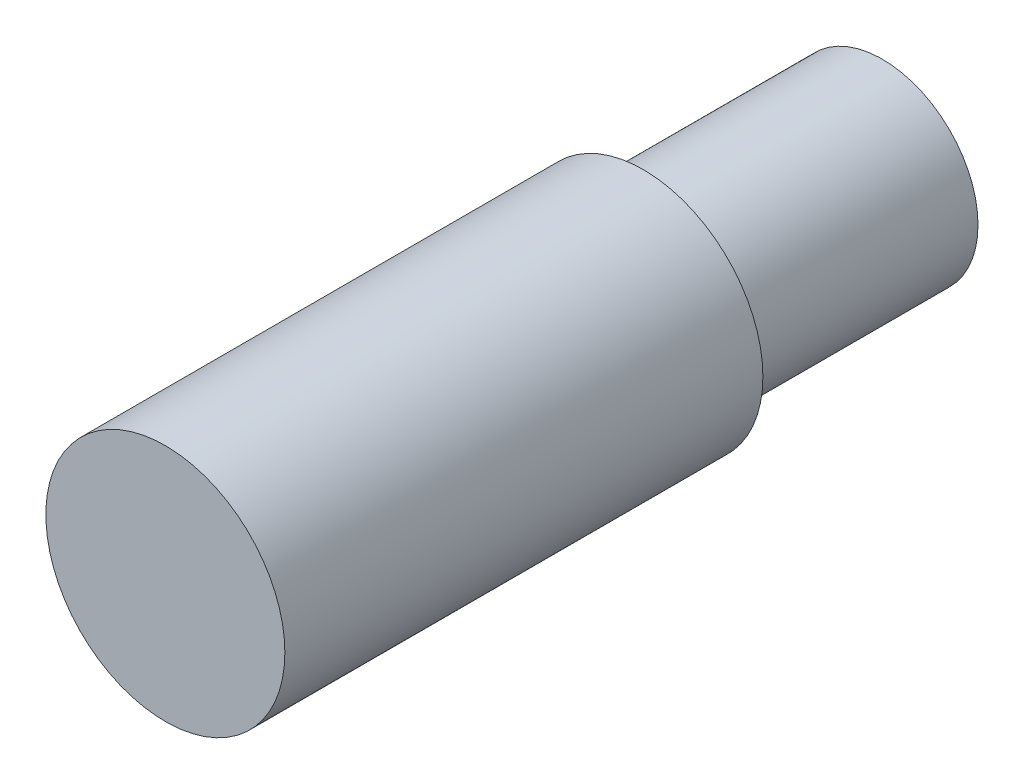
SolidWorks part; units mm, degrees
material "Aluminum Bronze"
ref_plane "Front Plane" through (0, 0, 0) normal (0, 0, 1) x (1, 0, 0)
ref_plane "Top Plane" through (0, 0, 0) normal (0, 1, 0) x (1, 0, 0)
ref_plane "Right Plane" through (0, 0, 0) normal (1, 0, 0) x (0, 0, -1)
sketch "Sketch1" plane through (0, 0, 0) normal (0, 0, 1) x (1, 0, 0)
  circle A0 centre (0, 0) radius 2
extrude "Extrude1" add sketch "Sketch1" along normal blind 5
sketch "Sketch2" plane through (0, 0, 5) normal (0, 0, 1) x (1, 0, 0)
  circle A0 centre (0, 0) radius 2.5
extrude "Extrude2" add sketch "Sketch2" along normal blind 10
